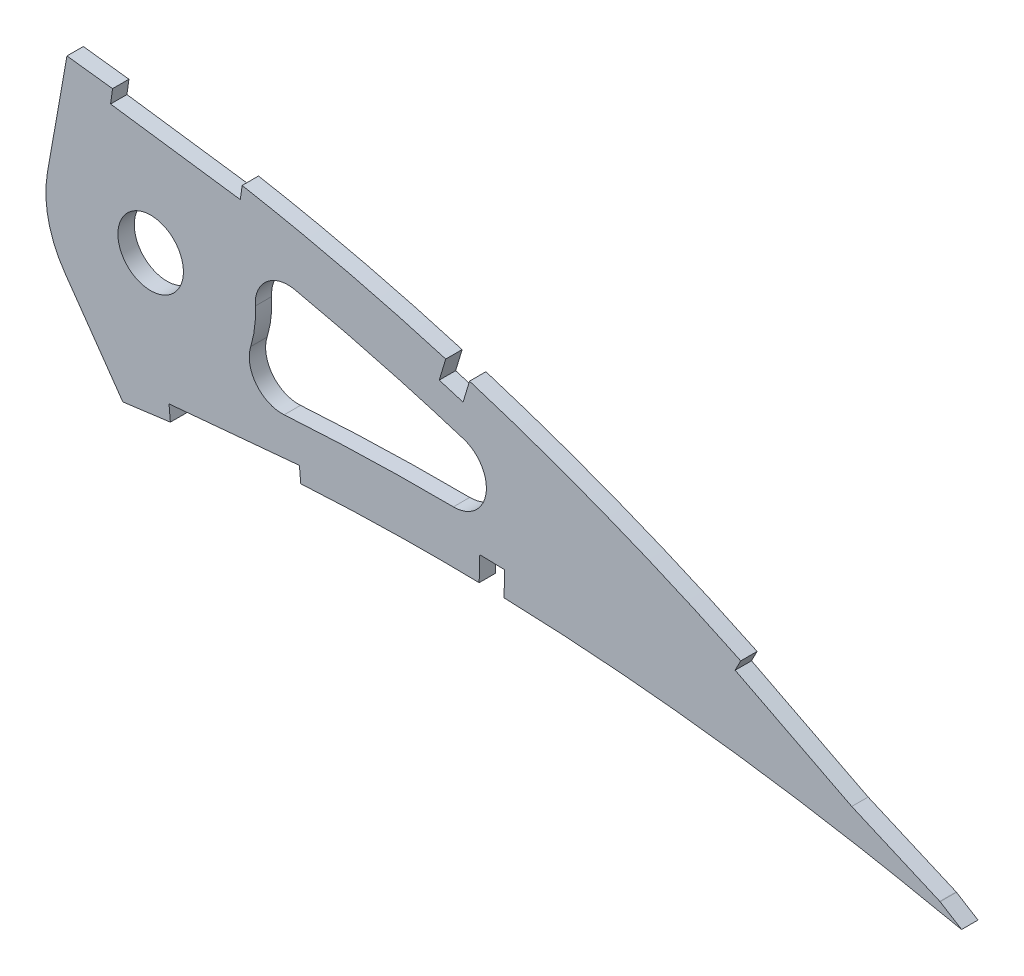
SolidWorks part; units mm, degrees
material "Plywood"
ref_plane "Front Plane" through (0, 0, 0) normal (0, 0, 1) x (1, 0, 0)
ref_plane "Top Plane" through (0, 0, 0) normal (0, 1, 0) x (1, 0, 0)
ref_plane "Right Plane" through (0, 0, 0) normal (1, 0, 0) x (0, 0, -1)
curve "Curve2"
  spline degree 3 poles (520.229, 0.8111, 0) (520.1892, 0.8357, 0) (520.0299, 0.9341, 0) (519.6711, 1.1542, 0) (519.0735, 1.5208, 0) (518.237, 2.0313, 0) (517.1622, 2.6844, 0) (515.8486, 3.4756, 0) (514.2969, 4.4021, 0) (512.5075, 5.4598, 0) (510.4807, 6.6436, 0) (508.2172, 7.9486, 0) (505.7172, 9.3676, 0) (502.9816, 10.8948, 0) (500.0114, 12.5227, 0) (496.8072, 14.2443, 0) (493.3701, 16.0505, 0) (489.7015, 17.9338, 0) (485.8019, 19.8836, 0) (481.6733, 21.8919, 0) (477.317, 23.9487, 0) (472.7345, 26.0429, 0) (467.9284, 28.1661, 0) (462.9001, 30.305, 0) (457.6524, 32.4505, 0) (452.1876, 34.5902, 0) (446.5089, 36.7144, 0) (440.6184, 38.8094, 0) (434.5207, 40.866, 0) (428.2186, 42.8708, 0) (421.7166, 44.813, 0) (415.0186, 46.68, 0) (408.1302, 48.4622, 0) (401.0555, 50.1466, 0) (393.8008, 51.7219, 0) (386.3718, 53.1787, 0) (378.7746, 54.5024, 0) (371.0303, 55.692, 0) (363.2636, 56.6815, 0) (355.5128, 57.652, 0) (347.7736, 58.5637, 0) (339.9398, 59.4368, 0) (332.019, 60.2663, 0) (324.019, 61.0497, 0) (315.9478, 61.7836, 0) (307.814, 62.4658, 0) (299.6253, 63.0925, 0) (291.3904, 63.6628, 0) (283.1174, 64.1714, 0) (274.8152, 64.6183, 0) (266.4922, 65.0001, 0) (258.157, 65.3142, 0) (249.8185, 65.5589, 0) (241.4854, 65.7316, 0) (233.1666, 65.8314, 0) (224.8708, 65.8555, 0) (216.6071, 65.8035, 0) (208.384, 65.6736, 0) (200.2107, 65.464, 0) (192.0958, 65.1743, 0) (184.048, 64.8046, 0) (176.0762, 64.3519, 0) (168.189, 63.8191, 0) (160.3952, 63.2038, 0) (152.7034, 62.506, 0) (145.1216, 61.7286, 0) (137.6583, 60.8693, 0) (130.3214, 59.9308, 0) (123.1191, 58.9147, 0) (116.0593, 57.8206, 0) (109.1496, 56.6517, 0) (102.3976, 55.409, 0) (95.8102, 54.0963, 0) (89.3948, 52.714, 0) (83.1581, 51.266, 0) (77.1065, 49.7551, 0) (71.2467, 48.1838, 0) (65.5845, 46.5561, 0) (60.1256, 44.8756, 0) (54.8764, 43.1442, 0) (49.8409, 41.3683, 0) (45.0253, 39.5493, 0) (40.4333, 37.6928, 0) (36.0702, 35.8014, 0) (31.9393, 33.8806, 0) (28.0452, 31.9329, 0) (24.3908, 29.9636, 0) (20.9797, 27.9757, 0) (17.8153, 25.973, 0) (14.8987, 23.9604, 0) (12.2341, 21.9394, 0) (9.8224, 19.9149, 0) (7.6651, 17.8901, 0) (5.7652, 15.8664, 0) (4.1228, 13.8473, 0) (2.7399, 11.8344, 0) (1.6168, 9.8297, 0) (0.7561, 7.8345, 0) (0.1568, 5.85, 0) (-0.1712, 3.8792, 0) (-0.2528, 1.9205, 0) (-0.0842, 0.6392, 0) (0, 0, 0) knots 0 0 0 0 0.000254 0.001015 0.002283 0.004057 0.006331 0.009105 0.012374 0.016134 0.02038 0.025106 0.030306 0.035972 0.0421 0.048678 0.055702 0.06316 0.071046 0.07935 0.088063 0.097176 0.106678 0.116562 0.126814 0.137428 0.148394 0.1597 0.171338 0.183298 0.19557 0.208144 0.221012 0.234162 0.247587 0.261277 0.275223 0.289414 0.303771 0.317689 0.331784 0.34604 0.360444 0.374983 0.38964 0.404403 0.419257 0.434187 0.449177 0.464215 0.479284 0.49437 0.509458 0.524532 0.539579 0.554583 0.56953 0.584403 0.599191 0.613877 0.628447 0.642889 0.657186 0.671326 0.685294 0.699078 0.712665 0.726043 0.739198 0.752118 0.764792 0.777208 0.789356 0.801224 0.812804 0.824083 0.835055 0.84571 0.856038 0.866034 0.875689 0.884998 0.893953 0.902553 0.910789 0.918661 0.926166 0.933303 0.940071 0.946475 0.952518 0.958205 0.963547 0.968557 0.97325 0.977651 0.981787 0.985694 0.989415 0.993001 0.996508 1 1 1 1
curve "Curve3"
  spline degree 3 poles (0, 0, 0) (0.1336, -0.6306, 0) (0.4014, -1.8948, 0) (1.129, -3.7148, 0) (2.0912, -5.4642, 0) (3.3081, -7.1386, 0) (4.7718, -8.7374, 0) (6.479, -10.2623, 0) (8.428, -11.7125, 0) (10.6162, -13.0874, 0) (13.0406, -14.3883, 0) (15.6982, -15.6145, 0) (18.5868, -16.7656, 0) (21.7032, -17.8401, 0) (25.0435, -18.8396, 0) (28.6046, -19.7616, 0) (32.3825, -20.6074, 0) (36.3735, -21.375, 0) (40.5732, -22.065, 0) (44.9774, -22.6771, 0) (49.5814, -23.2117, 0) (54.3808, -23.6676, 0) (59.3708, -24.0458, 0) (64.5464, -24.3466, 0) (69.9027, -24.5709, 0) (75.4344, -24.718, 0) (81.1363, -24.7899, 0) (87.003, -24.788, 0) (93.0289, -24.7115, 0) (99.2088, -24.5648, 0) (105.5368, -24.3469, 0) (112.0073, -24.0604, 0) (118.6142, -23.7083, 0) (125.3518, -23.2917, 0) (132.2141, -22.8125, 0) (139.1951, -22.2745, 0) (146.2885, -21.679, 0) (153.4882, -21.0296, 0) (160.7876, -20.3295, 0) (168.1806, -19.5808, 0) (175.6606, -18.7872, 0) (183.2209, -17.9512, 0) (190.8551, -17.0772, 0) (198.5563, -16.1668, 0) (206.3179, -15.2253, 0) (214.1326, -14.2544, 0) (221.9939, -13.2579, 0) (229.8947, -12.2404, 0) (237.8276, -11.2019, 0) (245.786, -10.1497, 0) (253.7621, -9.0829, 0) (261.7491, -8.0072, 0) (269.7395, -6.9257, 0) (277.7256, -5.8389, 0) (285.7003, -4.7513, 0) (293.6562, -3.6657, 0) (301.5856, -2.5824, 0) (309.4812, -1.5067, 0) (317.3352, -0.4385, 0) (325.1402, 0.6201, 0) (332.8888, 1.6659, 0) (340.5737, 2.6975, 0) (348.187, 3.7144, 0) (355.721, 4.7168, 0) (363.0553, 5.6745, 0) (370.1707, 6.6383, 0) (377.0913, 7.4284, 0) (383.9258, 8.1028, 0) (390.6811, 8.6557, 0) (397.3493, 9.0951, 0) (403.9227, 9.4241, 0) (410.3934, 9.6473, 0) (416.7532, 9.7713, 0) (422.9943, 9.7993, 0) (429.1081, 9.7402, 0) (435.0867, 9.5987, 0) (440.9216, 9.3813, 0) (446.6049, 9.0952, 0) (452.1283, 8.7483, 0) (457.4837, 8.3456, 0) (462.6634, 7.8966, 0) (467.6597, 7.4078, 0) (472.4647, 6.8849, 0) (477.0715, 6.3387, 0) (481.4727, 5.7729, 0) (485.6616, 5.1968, 0) (489.6316, 4.6162, 0) (493.3764, 4.0385, 0) (496.89, 3.4693, 0) (500.1667, 2.916, 0) (503.2016, 2.384, 0) (505.9892, 1.8782, 0) (508.5257, 1.4052, 0) (510.8062, 0.9673, 0) (512.8275, 0.5717, 0) (514.5859, 0.2202, 0) (516.0789, -0.0824, 0) (517.3037, -0.3347, 0) (518.2586, -0.5328, 0) (518.9417, -0.6767, 0) (519.3522, -0.7624, 0) (519.5346, -0.8013, 0) (519.5802, -0.8111, 0) knots 0 0 0 0 0.003638 0.007293 0.011028 0.014901 0.018963 0.023258 0.027821 0.032679 0.037853 0.043362 0.049215 0.055422 0.061989 0.068918 0.076211 0.083868 0.091887 0.100266 0.109 0.118085 0.127515 0.137285 0.147388 0.157816 0.168563 0.179619 0.190977 0.202627 0.21456 0.226767 0.239236 0.251959 0.264924 0.27812 0.291536 0.30516 0.318981 0.332985 0.347163 0.361499 0.375981 0.390597 0.405333 0.420175 0.43511 0.450124 0.465203 0.480333 0.495501 0.51069 0.525887 0.541078 0.556247 0.571382 0.586466 0.601485 0.616424 0.631269 0.646007 0.660621 0.675098 0.689423 0.703582 0.716908 0.730009 0.742952 0.755726 0.76832 0.780724 0.792927 0.804916 0.816679 0.828204 0.839475 0.850481 0.861208 0.871639 0.881763 0.891564 0.901027 0.910139 0.918884 0.927249 0.935221 0.942785 0.949928 0.956638 0.962904 0.968712 0.974054 0.978918 0.983297 0.98718 0.990561 0.993433 0.995791 0.99763 0.998946 0.999737 1 1 1 1
sketch "Sketch1" plane through (0, 0, 0) normal (0, 0, 1) x (1, 0, 0)
  line L1 (519.5802, -0.8111) -> (524.4049, -1.7687)
  line L2 (520.229, 0.8111) -> (524.4049, -1.7687)
  spline S0 degree 3 poles (-2903.7635, -749.124) (66.2436, 68.8235) (-8.6937, 20.855) (1.129, -3.7148) (2.0912, -5.4642) (3.3081, -7.1386) (4.7718, -8.7374) (6.479, -10.2623) (8.428, -11.7125) (10.6162, -13.0874) (13.0406, -14.3883) (15.6982, -15.6145) (18.5868, -16.7656) (21.7032, -17.8401) (25.0435, -18.8396) (28.6046, -19.7616) (32.3825, -20.6074) (36.3735, -21.375) (40.5732, -22.065) (44.9774, -22.6771) (49.5814, -23.2117) (54.3808, -23.6676) (59.3708, -24.0458) (64.5464, -24.3466) (69.9027, -24.5709) (75.4344, -24.718) (81.1363, -24.7899) (87.003, -24.788) (93.0289, -24.7115) (99.2088, -24.5648) (105.5368, -24.3469) (112.0073, -24.0604) (118.6142, -23.7083) (125.3518, -23.2917) (132.2141, -22.8125) (139.1951, -22.2745) (146.2885, -21.679) (153.4882, -21.0296) (160.7876, -20.3295) (168.1806, -19.5808) (175.6606, -18.7872) (183.2209, -17.9512) (190.8551, -17.0772) (198.5563, -16.1668) (206.3179, -15.2253) (214.1326, -14.2544) (221.9939, -13.2579) (229.8947, -12.2404) (237.8276, -11.2019) (245.786, -10.1497) (253.7621, -9.0829) (261.7491, -8.0072) (269.7395, -6.9257) (277.7256, -5.8389) (285.7003, -4.7513) (293.6562, -3.6657) (301.5856, -2.5824) (309.4812, -1.5067) (317.3352, -0.4385) (325.1402, 0.6201) (332.8888, 1.6659) (340.5737, 2.6975) (348.187, 3.7144) (355.721, 4.7168) (363.0553, 5.6745) (370.1707, 6.6383) (377.0913, 7.4284) (383.9258, 8.1028) (390.6811, 8.6557) (397.3493, 9.0951) (403.9227, 9.4241) (410.3934, 9.6473) (416.7532, 9.7713) (422.9943, 9.7993) (429.1081, 9.7402) (435.0867, 9.5987) (440.9216, 9.3813) (446.6049, 9.0952) (452.1283, 8.7483) (457.4837, 8.3456) (462.6634, 7.8966) (467.6597, 7.4078) (472.4647, 6.8849) (477.0715, 6.3387) (481.4727, 5.7729) (485.6616, 5.1968) (489.6316, 4.6162) (493.3764, 4.0385) (496.89, 3.4693) (500.1667, 2.916) (503.2016, 2.384) (505.9892, 1.8782) (508.5257, 1.4052) (510.8062, 0.9673) (512.8275, 0.5717) (514.5859, 0.2202) (516.0789, -0.0824) (517.3037, -0.3347) (518.2586, -0.5328) (518.9417, -0.6767) (537.0698, -4.4604) (553.3394, -15.9066) (1193.1482, 2921.6684) knots -0.137857 -0.137857 -0.137857 -0.137857 0.003638 0.007293 0.011028 0.014901 0.018963 0.023258 0.027821 0.032679 0.037853 0.043362 0.049215 0.055422 0.061989 0.068918 0.076211 0.083868 0.091887 0.100266 0.109 0.118085 0.127515 0.137285 0.147388 0.157816 0.168563 0.179619 0.190977 0.202627 0.21456 0.226767 0.239236 0.251959 0.264924 0.27812 0.291536 0.30516 0.318981 0.332985 0.347163 0.361499 0.375981 0.390597 0.405333 0.420175 0.43511 0.450124 0.465203 0.480333 0.495501 0.51069 0.525887 0.541078 0.556247 0.571382 0.586466 0.601485 0.616424 0.631269 0.646007 0.660621 0.675098 0.689423 0.703582 0.716908 0.730009 0.742952 0.755726 0.76832 0.780724 0.792927 0.804916 0.816679 0.828204 0.839475 0.850481 0.861208 0.871639 0.881763 0.891564 0.901027 0.910139 0.918884 0.927249 0.935221 0.942785 0.949928 0.956638 0.962904 0.968712 0.974054 0.978918 0.983297 0.98718 0.990561 0.993433 0.995791 0.99763 0.998946 0.999737 1.102307 1.102307 1.102307 1.102307 only from (0, 0) to (519.5802, -0.8111) construction
  spline S1 degree 3 poles (2144.5607, 2521.6799) (550.9976, -26.3511) (537.2872, -9.6513) (519.6711, 1.1542) (519.0735, 1.5208) (518.237, 2.0313) (517.1622, 2.6844) (515.8486, 3.4756) (514.2969, 4.4021) (512.5075, 5.4598) (510.4807, 6.6436) (508.2172, 7.9486) (505.7172, 9.3676) (502.9816, 10.8948) (500.0114, 12.5227) (496.8072, 14.2443) (493.3701, 16.0505) (489.7015, 17.9338) (485.8019, 19.8836) (481.6733, 21.8919) (477.317, 23.9487) (472.7345, 26.0429) (467.9284, 28.1661) (462.9001, 30.305) (457.6524, 32.4505) (452.1876, 34.5902) (446.5089, 36.7144) (440.6184, 38.8094) (434.5207, 40.866) (428.2186, 42.8708) (421.7166, 44.813) (415.0186, 46.68) (408.1302, 48.4622) (401.0555, 50.1466) (393.8008, 51.7219) (386.3718, 53.1787) (378.7746, 54.5024) (371.0303, 55.692) (363.2636, 56.6815) (355.5128, 57.652) (347.7736, 58.5637) (339.9398, 59.4368) (332.019, 60.2663) (324.019, 61.0497) (315.9478, 61.7836) (307.814, 62.4658) (299.6253, 63.0925) (291.3904, 63.6628) (283.1174, 64.1714) (274.8152, 64.6183) (266.4922, 65.0001) (258.157, 65.3142) (249.8185, 65.5589) (241.4854, 65.7316) (233.1666, 65.8314) (224.8708, 65.8555) (216.6071, 65.8035) (208.384, 65.6736) (200.2107, 65.464) (192.0958, 65.1743) (184.048, 64.8046) (176.0762, 64.3519) (168.189, 63.8191) (160.3952, 63.2038) (152.7034, 62.506) (145.1216, 61.7286) (137.6583, 60.8693) (130.3214, 59.9308) (123.1191, 58.9147) (116.0593, 57.8206) (109.1496, 56.6517) (102.3976, 55.409) (95.8102, 54.0963) (89.3948, 52.714) (83.1581, 51.266) (77.1065, 49.7551) (71.2467, 48.1838) (65.5845, 46.5561) (60.1256, 44.8756) (54.8764, 43.1442) (49.8409, 41.3683) (45.0253, 39.5493) (40.4333, 37.6928) (36.0702, 35.8014) (31.9393, 33.8806) (28.0452, 31.9329) (24.3908, 29.9636) (20.9797, 27.9757) (17.8153, 25.973) (14.8987, 23.9604) (12.2341, 21.9394) (9.8224, 19.9149) (7.6651, 17.8901) (5.7652, 15.8664) (4.1228, 13.8473) (2.7399, 11.8344) (1.6168, 9.8297) (0.7561, 7.8345) (0.1568, 5.85) (-0.1712, 3.8792) (-1.2714, -22.5145) (85.5395, -42.7616) (-2987.8188, -259.5241) knots -0.109813 -0.109813 -0.109813 -0.109813 0.000254 0.001015 0.002283 0.004057 0.006331 0.009105 0.012374 0.016134 0.02038 0.025106 0.030306 0.035972 0.0421 0.048678 0.055702 0.06316 0.071046 0.07935 0.088063 0.097176 0.106678 0.116562 0.126814 0.137428 0.148394 0.1597 0.171338 0.183298 0.19557 0.208144 0.221012 0.234162 0.247587 0.261277 0.275223 0.289414 0.303771 0.317689 0.331784 0.34604 0.360444 0.374983 0.38964 0.404403 0.419257 0.434187 0.449177 0.464215 0.479284 0.49437 0.509458 0.524532 0.539579 0.554583 0.56953 0.584403 0.599191 0.613877 0.628447 0.642889 0.657186 0.671326 0.685294 0.699078 0.712665 0.726043 0.739198 0.752118 0.764792 0.777208 0.789356 0.801224 0.812804 0.824083 0.835055 0.84571 0.856038 0.866034 0.875689 0.884998 0.893953 0.902553 0.910789 0.918661 0.926166 0.933303 0.940071 0.946475 0.952518 0.958205 0.963547 0.968557 0.97325 0.977651 0.981787 0.985694 0.989415 0.993001 0.996508 1.132043 1.132043 1.132043 1.132043 only from (520.229, 0.8111) to (0, 0) construction
  spline S2 degree 3 poles (0, 0) (0.1336, -0.6306) (0.4014, -1.8948) (1.129, -3.7148) (2.0912, -5.4642) (3.3081, -7.1386) (4.7718, -8.7374) (6.479, -10.2623) (8.428, -11.7125) (10.6162, -13.0874) (13.0406, -14.3883) (15.6982, -15.6145) (18.5868, -16.7656) (21.7032, -17.8401) (25.0435, -18.8396) (28.6046, -19.7616) (32.3825, -20.6074) (36.3735, -21.375) (40.5732, -22.065) (44.9774, -22.6771) (49.5814, -23.2117) (54.3808, -23.6676) (59.3708, -24.0458) (64.5464, -24.3466) (69.9027, -24.5709) (75.4344, -24.718) (81.1363, -24.7899) (87.003, -24.788) (93.0289, -24.7115) (99.2088, -24.5648) (105.5368, -24.3469) (112.0073, -24.0604) (118.6142, -23.7083) (125.3518, -23.2917) (132.2141, -22.8125) (139.1951, -22.2745) (146.2885, -21.679) (153.4882, -21.0296) (160.7876, -20.3295) (168.1806, -19.5808) (175.6606, -18.7872) (183.2209, -17.9512) (190.8551, -17.0772) (198.5563, -16.1668) (206.3179, -15.2253) (214.1326, -14.2544) (221.9939, -13.2579) (229.8947, -12.2404) (237.8276, -11.2019) (245.786, -10.1497) (253.7621, -9.0829) (261.7491, -8.0072) (269.7395, -6.9257) (277.7256, -5.8389) (285.7003, -4.7513) (293.6562, -3.6657) (301.5856, -2.5824) (309.4812, -1.5067) (317.3352, -0.4385) (325.1402, 0.6201) (332.8888, 1.6659) (340.5737, 2.6975) (348.187, 3.7144) (355.721, 4.7168) (363.0553, 5.6745) (370.1707, 6.6383) (377.0913, 7.4284) (383.9258, 8.1028) (390.6811, 8.6557) (397.3493, 9.0951) (403.9227, 9.4241) (410.3934, 9.6473) (416.7532, 9.7713) (422.9943, 9.7993) (429.1081, 9.7402) (435.0867, 9.5987) (440.9216, 9.3813) (446.6049, 9.0952) (452.1283, 8.7483) (457.4837, 8.3456) (462.6634, 7.8966) (467.6597, 7.4078) (472.4647, 6.8849) (477.0715, 6.3387) (481.4727, 5.7729) (485.6616, 5.1968) (489.6316, 4.6162) (493.3764, 4.0385) (496.89, 3.4693) (500.1667, 2.916) (503.2016, 2.384) (505.9892, 1.8782) (508.5257, 1.4052) (510.8062, 0.9673) (512.8275, 0.5717) (514.5859, 0.2202) (516.0789, -0.0824) (517.3037, -0.3347) (518.2586, -0.5328) (518.9417, -0.6767) (519.3522, -0.7624) (519.5346, -0.8013) (519.5802, -0.8111) knots 0 0 0 0 0.003638 0.007293 0.011028 0.014901 0.018963 0.023258 0.027821 0.032679 0.037853 0.043362 0.049215 0.055422 0.061989 0.068918 0.076211 0.083868 0.091887 0.100266 0.109 0.118085 0.127515 0.137285 0.147388 0.157816 0.168563 0.179619 0.190977 0.202627 0.21456 0.226767 0.239236 0.251959 0.264924 0.27812 0.291536 0.30516 0.318981 0.332985 0.347163 0.361499 0.375981 0.390597 0.405333 0.420175 0.43511 0.450124 0.465203 0.480333 0.495501 0.51069 0.525887 0.541078 0.556247 0.571382 0.586466 0.601485 0.616424 0.631269 0.646007 0.660621 0.675098 0.689423 0.703582 0.716908 0.730009 0.742952 0.755726 0.76832 0.780724 0.792927 0.804916 0.816679 0.828204 0.839475 0.850481 0.861208 0.871639 0.881763 0.891564 0.901027 0.910139 0.918884 0.927249 0.935221 0.942785 0.949928 0.956638 0.962904 0.968712 0.974054 0.978918 0.983297 0.98718 0.990561 0.993433 0.995791 0.99763 0.998946 0.999737 1 1 1 1
  spline S3 degree 3 poles (520.229, 0.8111) (520.1892, 0.8357) (520.0299, 0.9341) (519.6711, 1.1542) (519.0735, 1.5208) (518.237, 2.0313) (517.1622, 2.6844) (515.8486, 3.4756) (514.2969, 4.4021) (512.5075, 5.4598) (510.4807, 6.6436) (508.2172, 7.9486) (505.7172, 9.3676) (502.9816, 10.8948) (500.0114, 12.5227) (496.8072, 14.2443) (493.3701, 16.0505) (489.7015, 17.9338) (485.8019, 19.8836) (481.6733, 21.8919) (477.317, 23.9487) (472.7345, 26.0429) (467.9284, 28.1661) (462.9001, 30.305) (457.6524, 32.4505) (452.1876, 34.5902) (446.5089, 36.7144) (440.6184, 38.8094) (434.5207, 40.866) (428.2186, 42.8708) (421.7166, 44.813) (415.0186, 46.68) (408.1302, 48.4622) (401.0555, 50.1466) (393.8008, 51.7219) (386.3718, 53.1787) (378.7746, 54.5024) (371.0303, 55.692) (363.2636, 56.6815) (355.5128, 57.652) (347.7736, 58.5637) (339.9398, 59.4368) (332.019, 60.2663) (324.019, 61.0497) (315.9478, 61.7836) (307.814, 62.4658) (299.6253, 63.0925) (291.3904, 63.6628) (283.1174, 64.1714) (274.8152, 64.6183) (266.4922, 65.0001) (258.157, 65.3142) (249.8185, 65.5589) (241.4854, 65.7316) (233.1666, 65.8314) (224.8708, 65.8555) (216.6071, 65.8035) (208.384, 65.6736) (200.2107, 65.464) (192.0958, 65.1743) (184.048, 64.8046) (176.0762, 64.3519) (168.189, 63.8191) (160.3952, 63.2038) (152.7034, 62.506) (145.1216, 61.7286) (137.6583, 60.8693) (130.3214, 59.9308) (123.1191, 58.9147) (116.0593, 57.8206) (109.1496, 56.6517) (102.3976, 55.409) (95.8102, 54.0963) (89.3948, 52.714) (83.1581, 51.266) (77.1065, 49.7551) (71.2467, 48.1838) (65.5845, 46.5561) (60.1256, 44.8756) (54.8764, 43.1442) (49.8409, 41.3683) (45.0253, 39.5493) (40.4333, 37.6928) (36.0702, 35.8014) (31.9393, 33.8806) (28.0452, 31.9329) (24.3908, 29.9636) (20.9797, 27.9757) (17.8153, 25.973) (14.8987, 23.9604) (12.2341, 21.9394) (9.8224, 19.9149) (7.6651, 17.8901) (5.7652, 15.8664) (4.1228, 13.8473) (2.7399, 11.8344) (1.6168, 9.8297) (0.7561, 7.8345) (0.1568, 5.85) (-0.1712, 3.8792) (-0.2528, 1.9205) (-0.0842, 0.6392) (0, 0) knots 0 0 0 0 0.000254 0.001015 0.002283 0.004057 0.006331 0.009105 0.012374 0.016134 0.02038 0.025106 0.030306 0.035972 0.0421 0.048678 0.055702 0.06316 0.071046 0.07935 0.088063 0.097176 0.106678 0.116562 0.126814 0.137428 0.148394 0.1597 0.171338 0.183298 0.19557 0.208144 0.221012 0.234162 0.247587 0.261277 0.275223 0.289414 0.303771 0.317689 0.331784 0.34604 0.360444 0.374983 0.38964 0.404403 0.419257 0.434187 0.449177 0.464215 0.479284 0.49437 0.509458 0.524532 0.539579 0.554583 0.56953 0.584403 0.599191 0.613877 0.628447 0.642889 0.657186 0.671326 0.685294 0.699078 0.712665 0.726043 0.739198 0.752118 0.764792 0.777208 0.789356 0.801224 0.812804 0.824083 0.835055 0.84571 0.856038 0.866034 0.875689 0.884998 0.893953 0.902553 0.910789 0.918661 0.926166 0.933303 0.940071 0.946475 0.952518 0.958205 0.963547 0.968557 0.97325 0.977651 0.981787 0.985694 0.989415 0.993001 0.996508 1 1 1 1
extrude "Boss-Extrude1" add sketch "Sketch1" along normal blind 3.175
sketch "Sketch4" plane through (0, 0, 0) normal (0, 0, -1) x (-1, 0, 0)
  line L0 (-347.1309, 36.7611) -> (-350.9097, 58.1919)
  line L1 (-350.497, 21.5775) -> (-361.7496, 5.5072)
  line L2 (-520.229, 0.8111) -> (-524.4049, -1.7687)
  line L3 (-524.4049, -1.7687) -> (-519.5802, -0.8111)
  line L6 (-367.1422, 33.2326) -> (-394.958, 33.2326)
  circle A0 centre (-367.1422, 33.2326) radius 20.32
  circle A1 centre (-367.1422, 33.2326) radius 6.35
  spline S0 degree 1 poles (-521.6997, 9.1254) (-10.022, 1.7185) knots 0 0 1 1 construction
  spline S1 degree 1 poles (-10.022, 1.7185) (-514.8893, -7.8326) knots 0 0 1 1 construction
  spline S2 degree 3 poles (2987.4901, -259.5009) (-85.5334, -42.7602) (1.2713, -22.5136) (0.1712, 3.8792) (-0.1568, 5.85) (-0.7561, 7.8345) (-1.6168, 9.8297) (-2.7399, 11.8344) (-4.1228, 13.8473) (-5.7652, 15.8664) (-7.6651, 17.8901) (-9.8224, 19.9149) (-12.2341, 21.9394) (-14.8987, 23.9604) (-17.8153, 25.973) (-20.9797, 27.9757) (-24.3908, 29.9636) (-28.0452, 31.9329) (-31.9393, 33.8806) (-36.0702, 35.8014) (-40.4333, 37.6928) (-45.0253, 39.5493) (-49.8409, 41.3683) (-54.8764, 43.1442) (-60.1256, 44.8756) (-65.5845, 46.5561) (-71.2467, 48.1838) (-77.1065, 49.7551) (-83.1581, 51.266) (-89.3948, 52.714) (-95.8102, 54.0963) (-102.3976, 55.409) (-109.1496, 56.6517) (-116.0593, 57.8206) (-123.1191, 58.9147) (-130.3214, 59.9308) (-137.6583, 60.8693) (-145.1216, 61.7286) (-152.7034, 62.506) (-160.3952, 63.2038) (-168.189, 63.8191) (-176.0762, 64.3519) (-184.048, 64.8046) (-192.0958, 65.1743) (-200.2107, 65.464) (-208.384, 65.6736) (-216.6071, 65.8035) (-224.8708, 65.8555) (-233.1666, 65.8314) (-241.4854, 65.7316) (-249.8185, 65.5589) (-258.157, 65.3142) (-266.4922, 65.0001) (-274.8152, 64.6183) (-283.1174, 64.1714) (-291.3904, 63.6628) (-299.6253, 63.0925) (-307.814, 62.4658) (-315.9478, 61.7836) (-324.019, 61.0497) (-332.019, 60.2663) (-339.9398, 59.4368) (-347.7736, 58.5637) (-355.5128, 57.652) (-363.2636, 56.6815) (-371.0303, 55.692) (-378.7746, 54.5024) (-386.3718, 53.1787) (-393.8008, 51.7219) (-401.0555, 50.1466) (-408.1302, 48.4622) (-415.0186, 46.68) (-421.7166, 44.813) (-428.2186, 42.8708) (-434.5207, 40.866) (-440.6184, 38.8094) (-446.5089, 36.7144) (-452.1876, 34.5902) (-457.6524, 32.4505) (-462.9001, 30.305) (-467.9284, 28.1661) (-472.7345, 26.0429) (-477.317, 23.9487) (-481.6733, 21.8919) (-485.8019, 19.8836) (-489.7015, 17.9338) (-493.3701, 16.0505) (-496.8072, 14.2443) (-500.0114, 12.5227) (-502.9816, 10.8948) (-505.7172, 9.3676) (-508.2172, 7.9486) (-510.4807, 6.6436) (-512.5075, 5.4598) (-514.2969, 4.4021) (-515.8486, 3.4756) (-517.1622, 2.6844) (-518.237, 2.0313) (-519.0735, 1.5208) (-519.6711, 1.1542) (-537.2876, -9.6516) (-550.9983, -26.352) (-2144.6851, 2521.8788) knots -0.132038 -0.132038 -0.132038 -0.132038 0.003492 0.006999 0.010585 0.014306 0.018213 0.022349 0.02675 0.031443 0.036453 0.041795 0.047482 0.053525 0.059929 0.066697 0.073834 0.081339 0.089211 0.097447 0.106047 0.115002 0.124311 0.133966 0.143962 0.15429 0.164945 0.175917 0.187196 0.198776 0.210644 0.222792 0.235208 0.247882 0.260802 0.273957 0.287335 0.300922 0.314706 0.328674 0.342814 0.357111 0.371553 0.386123 0.400809 0.415597 0.43047 0.445417 0.460421 0.475468 0.490542 0.50563 0.520716 0.535785 0.550823 0.565813 0.580743 0.595597 0.61036 0.625017 0.639556 0.65396 0.668216 0.682311 0.696229 0.710586 0.724777 0.738723 0.752413 0.765838 0.778988 0.791856 0.80443 0.816702 0.828662 0.8403 0.851606 0.862572 0.873186 0.883438 0.893322 0.902824 0.911937 0.92065 0.928954 0.93684 0.944298 0.951322 0.9579 0.964028 0.969694 0.974894 0.97962 0.983866 0.987626 0.990895 0.993669 0.995943 0.997717 0.998985 0.999746 1.109816 1.109816 1.109816 1.109816 only from (0, 0) to (-520.229, 0.8111)
  spline S3 degree 3 poles (-1193.1472, 2921.6638) (-553.3393, -15.9066) (-537.0698, -4.4604) (-518.9417, -0.6767) (-518.2586, -0.5328) (-517.3037, -0.3347) (-516.0789, -0.0824) (-514.5859, 0.2202) (-512.8275, 0.5717) (-510.8062, 0.9673) (-508.5257, 1.4052) (-505.9892, 1.8782) (-503.2016, 2.384) (-500.1667, 2.916) (-496.89, 3.4693) (-493.3764, 4.0385) (-489.6316, 4.6162) (-485.6616, 5.1968) (-481.4727, 5.7729) (-477.0715, 6.3387) (-472.4647, 6.8849) (-467.6597, 7.4078) (-462.6634, 7.8966) (-457.4837, 8.3456) (-452.1283, 8.7483) (-446.6049, 9.0952) (-440.9216, 9.3813) (-435.0867, 9.5987) (-429.1081, 9.7402) (-422.9943, 9.7993) (-416.7532, 9.7713) (-410.3934, 9.6473) (-403.9227, 9.4241) (-397.3493, 9.0951) (-390.6811, 8.6557) (-383.9258, 8.1028) (-377.0913, 7.4284) (-370.1707, 6.6383) (-363.0553, 5.6745) (-355.721, 4.7168) (-348.187, 3.7144) (-340.5737, 2.6975) (-332.8888, 1.6659) (-325.1402, 0.6201) (-317.3352, -0.4385) (-309.4812, -1.5067) (-301.5856, -2.5824) (-293.6562, -3.6657) (-285.7003, -4.7513) (-277.7256, -5.8389) (-269.7395, -6.9257) (-261.7491, -8.0072) (-253.7621, -9.0829) (-245.786, -10.1497) (-237.8276, -11.2019) (-229.8947, -12.2404) (-221.9939, -13.2579) (-214.1326, -14.2544) (-206.3179, -15.2253) (-198.5563, -16.1668) (-190.8551, -17.0772) (-183.2209, -17.9512) (-175.6606, -18.7872) (-168.1806, -19.5808) (-160.7876, -20.3295) (-153.4882, -21.0296) (-146.2885, -21.679) (-139.1951, -22.2745) (-132.2141, -22.8125) (-125.3518, -23.2917) (-118.6142, -23.7083) (-112.0073, -24.0604) (-105.5368, -24.3469) (-99.2088, -24.5648) (-93.0289, -24.7115) (-87.003, -24.788) (-81.1363, -24.7899) (-75.4344, -24.718) (-69.9027, -24.5709) (-64.5464, -24.3466) (-59.3708, -24.0458) (-54.3808, -23.6676) (-49.5814, -23.2117) (-44.9774, -22.6771) (-40.5732, -22.065) (-36.3735, -21.375) (-32.3825, -20.6074) (-28.6046, -19.7616) (-25.0435, -18.8396) (-21.7032, -17.8401) (-18.5868, -16.7656) (-15.6982, -15.6145) (-13.0406, -14.3883) (-10.6162, -13.0874) (-8.428, -11.7125) (-6.479, -10.2623) (-4.7718, -8.7374) (-3.3081, -7.1386) (-2.0912, -5.4642) (-1.129, -3.7148) (8.6936, 20.8547) (-66.2416, 68.8223) (2903.6435, -749.0909) knots -0.102307 -0.102307 -0.102307 -0.102307 0.000263 0.001054 0.00237 0.004209 0.006567 0.009439 0.01282 0.016703 0.021082 0.025946 0.031288 0.037096 0.043362 0.050072 0.057215 0.064779 0.072751 0.081116 0.089861 0.098973 0.108436 0.118237 0.128361 0.138792 0.149519 0.160525 0.171796 0.183321 0.195084 0.207073 0.219276 0.23168 0.244274 0.257048 0.269991 0.283092 0.296418 0.310577 0.324902 0.339379 0.353993 0.368731 0.383576 0.398515 0.413534 0.428618 0.443753 0.458922 0.474113 0.48931 0.504499 0.519667 0.534797 0.549876 0.56489 0.579825 0.594667 0.609403 0.624019 0.638501 0.652837 0.667015 0.681019 0.69484 0.708464 0.72188 0.735076 0.748041 0.760764 0.773233 0.78544 0.797373 0.809023 0.820381 0.831437 0.842184 0.852612 0.862715 0.872485 0.881915 0.891 0.899734 0.908113 0.916132 0.923789 0.931082 0.938011 0.944578 0.950785 0.956638 0.962147 0.967321 0.972179 0.976742 0.981037 0.985099 0.988972 0.992707 0.996362 1.137855 1.137855 1.137855 1.137855 only from (-519.5802, -0.8111) to (0, 0)
  spline S4 degree 3 poles (0, 0) (0.0842, 0.6392) (0.2528, 1.9205) (0.1712, 3.8792) (-0.1568, 5.85) (-0.7561, 7.8345) (-1.6168, 9.8297) (-2.7399, 11.8344) (-4.1228, 13.8473) (-5.7652, 15.8664) (-7.6651, 17.8901) (-9.8224, 19.9149) (-12.2341, 21.9394) (-14.8987, 23.9604) (-17.8153, 25.973) (-20.9797, 27.9757) (-24.3908, 29.9636) (-28.0452, 31.9329) (-31.9393, 33.8806) (-36.0702, 35.8014) (-40.4333, 37.6928) (-45.0253, 39.5493) (-49.8409, 41.3683) (-54.8764, 43.1442) (-60.1256, 44.8756) (-65.5845, 46.5561) (-71.2467, 48.1838) (-77.1065, 49.7551) (-83.1581, 51.266) (-89.3948, 52.714) (-95.8102, 54.0963) (-102.3976, 55.409) (-109.1496, 56.6517) (-116.0593, 57.8206) (-123.1191, 58.9147) (-130.3214, 59.9308) (-137.6583, 60.8693) (-145.1216, 61.7286) (-152.7034, 62.506) (-160.3952, 63.2038) (-168.189, 63.8191) (-176.0762, 64.3519) (-184.048, 64.8046) (-192.0958, 65.1743) (-200.2107, 65.464) (-208.384, 65.6736) (-216.6071, 65.8035) (-224.8708, 65.8555) (-233.1666, 65.8314) (-241.4854, 65.7316) (-249.8185, 65.5589) (-258.157, 65.3142) (-266.4922, 65.0001) (-274.8152, 64.6183) (-283.1174, 64.1714) (-291.3904, 63.6628) (-299.6253, 63.0925) (-307.814, 62.4658) (-315.9478, 61.7836) (-324.019, 61.0497) (-332.019, 60.2663) (-339.9398, 59.4368) (-347.7736, 58.5637) (-355.5128, 57.652) (-363.2636, 56.6815) (-371.0303, 55.692) (-378.7746, 54.5024) (-386.3718, 53.1787) (-393.8008, 51.7219) (-401.0555, 50.1466) (-408.1302, 48.4622) (-415.0186, 46.68) (-421.7166, 44.813) (-428.2186, 42.8708) (-434.5207, 40.866) (-440.6184, 38.8094) (-446.5089, 36.7144) (-452.1876, 34.5902) (-457.6524, 32.4505) (-462.9001, 30.305) (-467.9284, 28.1661) (-472.7345, 26.0429) (-477.317, 23.9487) (-481.6733, 21.8919) (-485.8019, 19.8836) (-489.7015, 17.9338) (-493.3701, 16.0505) (-496.8072, 14.2443) (-500.0114, 12.5227) (-502.9816, 10.8948) (-505.7172, 9.3676) (-508.2172, 7.9486) (-510.4807, 6.6436) (-512.5075, 5.4598) (-514.2969, 4.4021) (-515.8486, 3.4756) (-517.1622, 2.6844) (-518.237, 2.0313) (-519.0735, 1.5208) (-519.6711, 1.1542) (-520.0299, 0.9341) (-520.1892, 0.8357) (-520.229, 0.8111) knots 0 0 0 0 0.003492 0.006999 0.010585 0.014306 0.018213 0.022349 0.02675 0.031443 0.036453 0.041795 0.047482 0.053525 0.059929 0.066697 0.073834 0.081339 0.089211 0.097447 0.106047 0.115002 0.124311 0.133966 0.143962 0.15429 0.164945 0.175917 0.187196 0.198776 0.210644 0.222792 0.235208 0.247882 0.260802 0.273957 0.287335 0.300922 0.314706 0.328674 0.342814 0.357111 0.371553 0.386123 0.400809 0.415597 0.43047 0.445417 0.460421 0.475468 0.490542 0.50563 0.520716 0.535785 0.550823 0.565813 0.580743 0.595597 0.61036 0.625017 0.639556 0.65396 0.668216 0.682311 0.696229 0.710586 0.724777 0.738723 0.752413 0.765838 0.778988 0.791856 0.80443 0.816702 0.828662 0.8403 0.851606 0.862572 0.873186 0.883438 0.893322 0.902824 0.911937 0.92065 0.928954 0.93684 0.944298 0.951322 0.9579 0.964028 0.969694 0.974894 0.97962 0.983866 0.987626 0.990895 0.993669 0.995943 0.997717 0.998985 0.999746 1 1 1 1
  spline S5 degree 3 poles (-519.5802, -0.8111) (-519.5346, -0.8013) (-519.3522, -0.7624) (-518.9417, -0.6767) (-518.2586, -0.5328) (-517.3037, -0.3347) (-516.0789, -0.0824) (-514.5859, 0.2202) (-512.8275, 0.5717) (-510.8062, 0.9673) (-508.5257, 1.4052) (-505.9892, 1.8782) (-503.2016, 2.384) (-500.1667, 2.916) (-496.89, 3.4693) (-493.3764, 4.0385) (-489.6316, 4.6162) (-485.6616, 5.1968) (-481.4727, 5.7729) (-477.0715, 6.3387) (-472.4647, 6.8849) (-467.6597, 7.4078) (-462.6634, 7.8966) (-457.4837, 8.3456) (-452.1283, 8.7483) (-446.6049, 9.0952) (-440.9216, 9.3813) (-435.0867, 9.5987) (-429.1081, 9.7402) (-422.9943, 9.7993) (-416.7532, 9.7713) (-410.3934, 9.6473) (-403.9227, 9.4241) (-397.3493, 9.0951) (-390.6811, 8.6557) (-383.9258, 8.1028) (-377.0913, 7.4284) (-370.1707, 6.6383) (-363.0553, 5.6745) (-355.721, 4.7168) (-348.187, 3.7144) (-340.5737, 2.6975) (-332.8888, 1.6659) (-325.1402, 0.6201) (-317.3352, -0.4385) (-309.4812, -1.5067) (-301.5856, -2.5824) (-293.6562, -3.6657) (-285.7003, -4.7513) (-277.7256, -5.8389) (-269.7395, -6.9257) (-261.7491, -8.0072) (-253.7621, -9.0829) (-245.786, -10.1497) (-237.8276, -11.2019) (-229.8947, -12.2404) (-221.9939, -13.2579) (-214.1326, -14.2544) (-206.3179, -15.2253) (-198.5563, -16.1668) (-190.8551, -17.0772) (-183.2209, -17.9512) (-175.6606, -18.7872) (-168.1806, -19.5808) (-160.7876, -20.3295) (-153.4882, -21.0296) (-146.2885, -21.679) (-139.1951, -22.2745) (-132.2141, -22.8125) (-125.3518, -23.2917) (-118.6142, -23.7083) (-112.0073, -24.0604) (-105.5368, -24.3469) (-99.2088, -24.5648) (-93.0289, -24.7115) (-87.003, -24.788) (-81.1363, -24.7899) (-75.4344, -24.718) (-69.9027, -24.5709) (-64.5464, -24.3466) (-59.3708, -24.0458) (-54.3808, -23.6676) (-49.5814, -23.2117) (-44.9774, -22.6771) (-40.5732, -22.065) (-36.3735, -21.375) (-32.3825, -20.6074) (-28.6046, -19.7616) (-25.0435, -18.8396) (-21.7032, -17.8401) (-18.5868, -16.7656) (-15.6982, -15.6145) (-13.0406, -14.3883) (-10.6162, -13.0874) (-8.428, -11.7125) (-6.479, -10.2623) (-4.7718, -8.7374) (-3.3081, -7.1386) (-2.0912, -5.4642) (-1.129, -3.7148) (-0.4014, -1.8948) (-0.1336, -0.6306) (0, 0) knots 0 0 0 0 0.000263 0.001054 0.00237 0.004209 0.006567 0.009439 0.01282 0.016703 0.021082 0.025946 0.031288 0.037096 0.043362 0.050072 0.057215 0.064779 0.072751 0.081116 0.089861 0.098973 0.108436 0.118237 0.128361 0.138792 0.149519 0.160525 0.171796 0.183321 0.195084 0.207073 0.219276 0.23168 0.244274 0.257048 0.269991 0.283092 0.296418 0.310577 0.324902 0.339379 0.353993 0.368731 0.383576 0.398515 0.413534 0.428618 0.443753 0.458922 0.474113 0.48931 0.504499 0.519667 0.534797 0.549876 0.56489 0.579825 0.594667 0.609403 0.624019 0.638501 0.652837 0.667015 0.681019 0.69484 0.708464 0.72188 0.735076 0.748041 0.760764 0.773233 0.78544 0.797373 0.809023 0.820381 0.831437 0.842184 0.852612 0.862715 0.872485 0.881915 0.891 0.899734 0.908113 0.916132 0.923789 0.931082 0.938011 0.944578 0.950785 0.956638 0.962147 0.967321 0.972179 0.976742 0.981037 0.985099 0.988972 0.992707 0.996362 1 1 1 1
  spline S6 degree 3 poles (-521.6997, 9.1254) (-521.5185, 9.1641) (-521.1414, 9.2431) (-520.5013, 9.3777) (-519.6014, 9.5652) (-518.5867, 9.7745) (-516.5017, 10.2002) (-512.0338, 11.0895) (-502.3328, 12.9034) (-482.8666, 16.0553) (-454.7955, 19.1487) (-426.5367, 20.1772) (-403.9091, 19.6864) (-389.7949, 18.8264) (-379.9243, 17.9283) (-374.3105, 17.3355) (-370.0824, 16.8486) (-365.8505, 16.3062) (-361.7465, 15.7537) (-357.6653, 15.2168) (-352.1695, 14.4949) (-345.3171, 13.5814) (-334.359, 12.1168) (-315.179, 9.5288) (-287.8082, 5.789) (-254.9835, 1.3131) (-222.1895, -3.0348) (-189.4106, -7.0959) (-156.654, -10.6508) (-129.3813, -12.9449) (-107.6083, -14.1485) (-91.3205, -14.6521) (-75.1074, -14.6475) (-61.7108, -14.0897) (-51.1341, -13.1896) (-43.3067, -12.2396) (-35.6411, -10.9589) (-28.237, -9.2636) (-21.2892, -7.0583) (-16.2032, -4.6866) (-13.0461, -2.5478) (-11.6056, -1.201) (-10.836, -0.2227) (-10.5202, 0.2936) (-10.2886, 0.7695) (-10.2055, 0.9824) (-10.1785, 1.0643) (-10.1577, 1.1349) (-10.1105, 1.3225) (-10.0643, 1.5249) (-10.0354, 1.6565) (-10.022, 1.7185) knots 0 0 0 0 0.000976 0.001952 0.003903 0.005855 0.007806 0.015612 0.031224 0.062448 0.124896 0.187344 0.218569 0.249793 0.265405 0.273211 0.281017 0.288823 0.296629 0.304435 0.312241 0.327853 0.343465 0.374689 0.437137 0.499585 0.562033 0.624482 0.68693 0.749378 0.780602 0.811826 0.84305 0.874274 0.889886 0.905498 0.92111 0.936722 0.952334 0.967946 0.975753 0.983559 0.987462 0.991365 0.993316 0.995268 0.996243 0.997219 0.998195 0.998683 0.999171 0.999171 0.999171 0.999171
  spline S7 degree 3 poles (-10.022, 1.7185) (-10.0137, 1.7838) (-9.9964, 1.9227) (-9.9722, 2.1338) (-9.9548, 2.3267) (-9.9521, 2.385) (-9.9503, 2.4853) (-9.9613, 2.7344) (-10.0122, 3.1442) (-10.0839, 3.5102) (-10.2224, 4.0331) (-10.6171, 5.1175) (-11.6184, 6.9252) (-14.1026, 10.0907) (-18.4256, 14.0534) (-24.6526, 18.4028) (-31.4923, 22.3392) (-38.7272, 25.9013) (-46.2345, 29.1355) (-56.5074, 33.06) (-69.7207, 37.3231) (-85.9449, 41.5978) (-102.4194, 45.1568) (-124.6274, 49.0726) (-152.7038, 52.5874) (-186.6719, 55.0054) (-220.784, 55.8886) (-254.9542, 55.4386) (-289.1234, 53.7977) (-317.5664, 51.5306) (-337.4323, 49.5018) (-348.7883, 48.2227) (-357.2614, 47.1962) (-365.8396, 46.1279) (-374.0765, 44.9754) (-382.3862, 43.5815) (-393.3717, 41.4855) (-407.0282, 38.3742) (-428.6204, 32.3912) (-455.0706, 23.0586) (-480.6155, 11.4116) (-497.9507, 2.1395) (-506.4753, -2.765) (-510.6983, -5.2786) (-512.8069, -6.557) (-513.8432, -7.1901) (-514.4641, -7.5709) (-514.7453, -7.7437) (-514.8893, -7.8326) knots 0.000796 0.000796 0.000796 0.000796 0.001284 0.001772 0.002748 0.003724 0.004699 0.006651 0.008603 0.010554 0.012506 0.016409 0.024215 0.032021 0.047634 0.063247 0.078859 0.094472 0.110084 0.125697 0.156922 0.188147 0.219372 0.250597 0.313047 0.375498 0.437948 0.500398 0.562848 0.625299 0.656524 0.672136 0.687749 0.703361 0.718974 0.734587 0.750199 0.781424 0.812649 0.8751 0.93755 0.968775 0.984387 0.992194 0.996097 0.998048 0.999024 1 1 1 1
  dimension "D3" = 40.64
  dimension "D4" = 80
  dimension "D5" = 55
  dimension "D1" = 0
  dimension "D2" = 10.16
extrude "Cut-Extrude3" cut sketch "Sketch4" against normal through all
sketch "Sketch5" plane through (0, 0, 3.175) normal (0, 0, 1) x (1, 0, 0)
  line L1 (384.9613, 54.0165) -> (359.8038, 57.4907)
  line L3 (395.9844, 11.9659) -> (370.6988, 9.6537)
  line L5 (429.1179, 43.0703) -> (424.4993, 44.4641)
  line L7 (435.787, 14.3413) -> (430.9639, 14.4592)
  line L9 (504.4525, 11.1152) -> (481.935, 22.6423)
  line L11 (527.6665, 1.0588) -> (504.4525, 11.1152)
  line L13 (526.4044, -1.8545) -> (527.6665, 1.0588)
  line L15 (435.6691, 9.5183) -> (435.787, 14.3413)
  line L17 (396.2734, 8.8052) -> (395.9844, 11.9659)
  line L19 (427.7241, 38.4518) -> (429.1179, 43.0703)
  line L21 (384.527, 50.8718) -> (384.9613, 54.0165)
  line L23 (359.3695, 54.346) -> (384.527, 50.8718)
  line L25 (370.9878, 6.493) -> (396.2734, 8.8052)
  line L27 (423.1056, 39.8456) -> (427.7241, 38.4518)
  line L29 (430.8461, 9.6361) -> (435.6691, 9.5183)
  line L31 (480.4883, 19.8161) -> (503.0975, 8.2421)
  line L33 (503.0975, 8.2421) -> (526.4044, -1.8545)
  line L35 (424.4993, 44.4641) -> (423.1056, 39.8456)
  line L37 (359.8038, 57.4907) -> (359.3695, 54.346)
  line L39 (481.935, 22.6423) -> (480.4883, 19.8161)
  line L41 (430.9639, 14.4592) -> (430.8461, 9.6361)
  line L43 (370.6988, 9.6537) -> (370.9878, 6.493)
extrude "Cut-Extrude4" cut sketch "Sketch5" against normal blind 7.62
fillet "Fillet1" radius 6.35 3 edges at (466.3825, 17.7386, 1.5875) (380.5614, 17.9739, 1.5875) (384.9122, 43.088, 1.5875)
move or copy body "Body-Move/Copy1" [suppressed] bodies to move or copy 118 parameters "D1"=0, "D2"=0, "D3"=0
